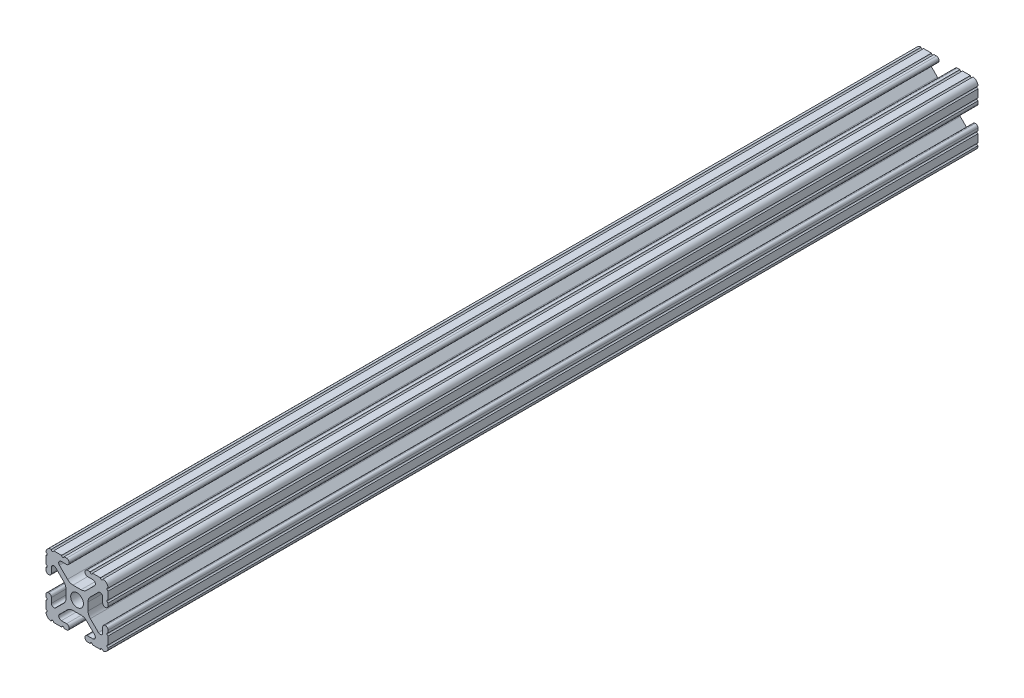
SolidWorks part; units mm, degrees
ref_plane "Front Plane" through (0, 0, 0) normal (0, 0, 1) x (1, 0, 0)
ref_plane "Top Plane" through (0, 0, 0) normal (0, 1, 0) x (1, 0, 0)
ref_plane "Right Plane" through (0, 0, 0) normal (1, 0, 0) x (0, 0, -1)
sketch "Sketch1" plane through (0, 0, 0) normal (0, 0, 1) x (1, 0, 0)
  line L88 (-7.1797, -8.6452) -> (-3.9523, -5.4237)
  line L89 (-1.7093, -4.4958) -> (1.7093, -4.4958)
  line L90 (3.9523, -5.4237) -> (7.1797, -8.6452)
  line L91 (6.4164, -10.4902) -> (4.2875, -10.4902)
  line L92 (3.2385, -11.5392) -> (3.2385, -11.651)
  line L93 (4.2875, -12.7) -> (5.3171, -12.7)
  line L94 (6.3331, -12.7) -> (9.5504, -12.7)
  line L95 (12.7, -9.5504) -> (12.7, -6.3331)
  line L96 (12.7, -5.3171) -> (12.7, -4.2875)
  line L97 (11.651, -3.2385) -> (11.5392, -3.2385)
  line L98 (10.4902, -4.2875) -> (10.4902, -6.4021)
  line L99 (8.7371, -7.1294) -> (5.441, -3.8408)
  line L100 (4.5085, -1.5932) -> (4.5085, 1.5932)
  line L101 (5.441, 3.8408) -> (8.7371, 7.1294)
  line L102 (10.4902, 6.4021) -> (10.4902, 4.2875)
  line L103 (11.5392, 3.2385) -> (11.651, 3.2385)
  line L104 (12.7, 4.2875) -> (12.7, 5.3171)
  line L105 (12.7, 6.3331) -> (12.7, 9.5504)
  line L106 (9.5504, 12.7) -> (6.3331, 12.7)
  line L107 (5.3171, 12.7) -> (4.2875, 12.7)
  line L108 (3.2385, 11.651) -> (3.2385, 11.5392)
  line L109 (4.2875, 10.4902) -> (6.4768, 10.4902)
  line L110 (7.207, 8.7244) -> (3.8983, 5.4232)
  line L111 (1.6558, 4.4958) -> (-1.6558, 4.4958)
  line L112 (-3.8983, 5.4232) -> (-7.207, 8.7244)
  line L113 (-6.4768, 10.4902) -> (-4.2875, 10.4902)
  line L114 (-3.2385, 11.5392) -> (-3.2385, 11.651)
  line L115 (-4.2875, 12.7) -> (-5.3171, 12.7)
  line L116 (-6.3331, 12.7) -> (-9.5504, 12.7)
  line L117 (-12.7, 9.5504) -> (-12.7, 6.3331)
  line L118 (-12.7, 5.3171) -> (-12.7, 4.2875)
  line L119 (-11.651, 3.2385) -> (-11.5392, 3.2385)
  line L120 (-10.4902, 4.2875) -> (-10.4902, 6.4021)
  line L121 (-8.7371, 7.1294) -> (-5.441, 3.8408)
  line L122 (-4.5085, 1.5932) -> (-4.5085, -1.5932)
  line L123 (-5.441, -3.8408) -> (-8.7371, -7.1294)
  line L124 (-10.4902, -6.4021) -> (-10.4902, -4.2875)
  line L125 (-11.5392, -3.2385) -> (-11.651, -3.2385)
  line L126 (-12.7, -4.2875) -> (-12.7, -5.3171)
  line L127 (-12.7, -6.3331) -> (-12.7, -9.5504)
  line L128 (-9.5504, -12.7) -> (-6.3331, -12.7)
  line L129 (-5.3171, -12.7) -> (-4.2875, -12.7)
  line L130 (-3.2385, -11.651) -> (-3.2385, -11.5392)
  line L131 (-4.2875, -10.4902) -> (-6.4164, -10.4902)
  circle A1 centre (0, 0) radius 2.6035
  arc A104 (-7.1797, -8.6452) -> (-6.4164, -10.4902) centre (-6.4164, -9.4098) ccw
  arc A105 (-1.7093, -4.4958) -> (-3.9523, -5.4237) centre (-1.7093, -7.6708) ccw
  arc A106 (3.9523, -5.4237) -> (1.7093, -4.4958) centre (1.7093, -7.6708) ccw
  arc A107 (6.4164, -10.4902) -> (7.1797, -8.6452) centre (6.4164, -9.4098) ccw
  arc A108 (4.2875, -10.4902) -> (3.2385, -11.5392) centre (4.2875, -11.5392) ccw
  arc A109 (3.2385, -11.651) -> (4.2875, -12.7) centre (4.2875, -11.651) ccw
  arc A110 (6.3331, -12.7) -> (5.3171, -12.7) centre (5.8251, -12.7) ccw
  arc A111 (10.5664, -12.6998) -> (9.5504, -12.7) centre (10.0584, -12.7) ccw
  arc A112 (10.5664, -12.6998) -> (12.6998, -10.5664) centre (10.5918, -10.5918) ccw
  arc A113 (12.7, -9.5504) -> (12.6998, -10.5664) centre (12.7, -10.0584) ccw
  arc A114 (12.7, -5.3171) -> (12.7, -6.3331) centre (12.7, -5.8251) ccw
  arc A115 (12.7, -4.2875) -> (11.651, -3.2385) centre (11.651, -4.2875) ccw
  arc A116 (11.5392, -3.2385) -> (10.4902, -4.2875) centre (11.5392, -4.2875) ccw
  arc A117 (8.7371, -7.1294) -> (10.4902, -6.4021) centre (9.4628, -6.4021) ccw
  arc A118 (4.5085, -1.5932) -> (5.441, -3.8408) centre (7.6835, -1.5932) ccw
  arc A119 (5.441, 3.8408) -> (4.5085, 1.5932) centre (7.6835, 1.5932) ccw
  arc A120 (10.4902, 6.4021) -> (8.7371, 7.1294) centre (9.4628, 6.4021) ccw
  arc A121 (10.4902, 4.2875) -> (11.5392, 3.2385) centre (11.5392, 4.2875) ccw
  arc A122 (11.651, 3.2385) -> (12.7, 4.2875) centre (11.651, 4.2875) ccw
  arc A123 (12.7, 6.3331) -> (12.7, 5.3171) centre (12.7, 5.8251) ccw
  arc A124 (12.6998, 10.5664) -> (12.7, 9.5504) centre (12.7, 10.0584) ccw
  arc A125 (12.6998, 10.5664) -> (10.5664, 12.6998) centre (10.5918, 10.5918) ccw
  arc A126 (9.5504, 12.7) -> (10.5664, 12.6998) centre (10.0584, 12.7) ccw
  arc A127 (5.3171, 12.7) -> (6.3331, 12.7) centre (5.8251, 12.7) ccw
  arc A128 (4.2875, 12.7) -> (3.2385, 11.651) centre (4.2875, 11.651) ccw
  arc A129 (3.2385, 11.5392) -> (4.2875, 10.4902) centre (4.2875, 11.5392) ccw
  arc A130 (7.207, 8.7244) -> (6.4768, 10.4902) centre (6.4768, 9.4563) ccw
  arc A131 (1.6558, 4.4958) -> (3.8983, 5.4232) centre (1.6558, 7.6708) ccw
  arc A132 (-3.8983, 5.4232) -> (-1.6558, 4.4958) centre (-1.6558, 7.6708) ccw
  arc A133 (-6.4768, 10.4902) -> (-7.207, 8.7244) centre (-6.4768, 9.4563) ccw
  arc A134 (-4.2875, 10.4902) -> (-3.2385, 11.5392) centre (-4.2875, 11.5392) ccw
  arc A135 (-3.2385, 11.651) -> (-4.2875, 12.7) centre (-4.2875, 11.651) ccw
  arc A136 (-6.3331, 12.7) -> (-5.3171, 12.7) centre (-5.8251, 12.7) ccw
  arc A137 (-10.5664, 12.6998) -> (-9.5504, 12.7) centre (-10.0584, 12.7) ccw
  arc A138 (-10.5664, 12.6998) -> (-12.6998, 10.5664) centre (-10.5918, 10.5918) ccw
  arc A139 (-12.7, 9.5504) -> (-12.6998, 10.5664) centre (-12.7, 10.0584) ccw
  arc A140 (-12.7, 5.3171) -> (-12.7, 6.3331) centre (-12.7, 5.8251) ccw
  arc A141 (-12.7, 4.2875) -> (-11.651, 3.2385) centre (-11.651, 4.2875) ccw
  arc A142 (-11.5392, 3.2385) -> (-10.4902, 4.2875) centre (-11.5392, 4.2875) ccw
  arc A143 (-8.7371, 7.1294) -> (-10.4902, 6.4021) centre (-9.4628, 6.4021) ccw
  arc A144 (-4.5085, 1.5932) -> (-5.441, 3.8408) centre (-7.6835, 1.5932) ccw
  arc A145 (-5.441, -3.8408) -> (-4.5085, -1.5932) centre (-7.6835, -1.5932) ccw
  arc A146 (-10.4902, -6.4021) -> (-8.7371, -7.1294) centre (-9.4628, -6.4021) ccw
  arc A147 (-10.4902, -4.2875) -> (-11.5392, -3.2385) centre (-11.5392, -4.2875) ccw
  arc A148 (-11.651, -3.2385) -> (-12.7, -4.2875) centre (-11.651, -4.2875) ccw
  arc A149 (-12.7, -6.3331) -> (-12.7, -5.3171) centre (-12.7, -5.8251) ccw
  arc A150 (-12.6998, -10.5664) -> (-12.7, -9.5504) centre (-12.7, -10.0584) ccw
  arc A151 (-12.6998, -10.5664) -> (-10.5664, -12.6998) centre (-10.5918, -10.5918) ccw
  arc A152 (-9.5504, -12.7) -> (-10.5664, -12.6998) centre (-10.0584, -12.7) ccw
  arc A153 (-5.3171, -12.7) -> (-6.3331, -12.7) centre (-5.8251, -12.7) ccw
  arc A154 (-4.2875, -12.7) -> (-3.2385, -11.651) centre (-4.2875, -11.651) ccw
  arc A155 (-3.2385, -11.5392) -> (-4.2875, -10.4902) centre (-4.2875, -11.5392) ccw
extrude "Boss-Extrude1" add sketch "Sketch1" along normal mid plane 355.8
